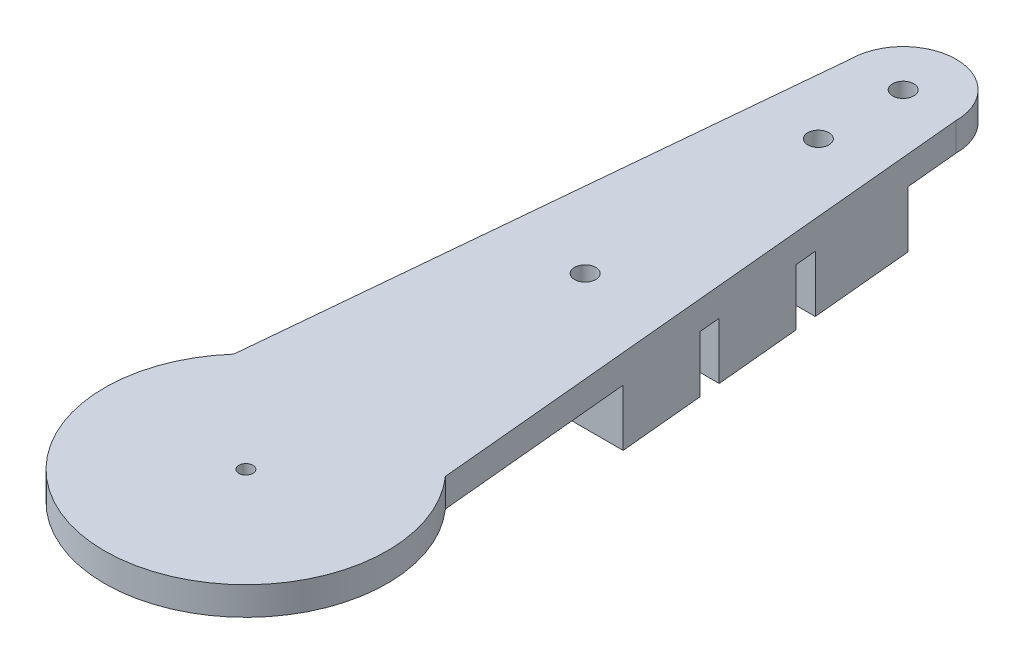
SolidWorks part; units mm, degrees
ref_plane "Front Plane" through (0, 0, 0) normal (0, 0, 1) x (1, 0, 0)
ref_plane "Top Plane" through (0, 0, 0) normal (0, 1, 0) x (1, 0, 0)
ref_plane "Right Plane" through (0, 0, 0) normal (1, 0, 0) x (0, 0, -1)
sketch "Sketch1" plane through (0, 0, 0) normal (0, 0, 1) x (1, 0, 0)
  line L0 (0, -2) -> (10.5, -2)
  line L1 (0, 0) -> (20, 0)
  line L2 (0, 0) -> (0, -2)
  line L3 (10.5, -4) -> (20, -4)
  line L4 (20, 0) -> (20, -4)
  line L5 (10.5, -2) -> (10.5, -4)
  dimension "D1" = 4
  dimension "D2" = 20
  dimension "D3" = 2
  dimension "D4" = 10.5
revolve "Revolve1" add sketch "Sketch1" angle 360 about L2
sketch "Sketch2" plane through (0, 0, 0) normal (0, 1, 0) x (1, 0, 0)
  circle A0 centre (0, 0) radius 1
  dimension "D1" = 2
extrude "Cut-Extrude1" cut sketch "Sketch2" against normal blind 10
sketch "Sketch3" plane through (0, 0, 0) normal (0, 1, 0) x (1, 0, 0)
  line L0 (-7.5, 93) -> (-15, 13)
  line L1 (-15, 13) -> (15, 13)
  line L3 (-7.5, 93) -> (7.5, 93)
  line L5 (7.5, 93) -> (15, 13)
  dimension "D1" = 80
  dimension "D2" = 30
  dimension "D3" = 13
  dimension "D4" = 15
  dimension "D5" = 7.5
extrude "Boss-Extrude1" add sketch "Sketch3" against normal up to surface (4 mm away) up to face at (-20, -4, 0)
sketch "Sketch4" plane through (0, -4, 0) normal (0, -1, 0) x (1, 0, 0)
  line L0 (-12.375, -41) -> (12.375, -41)
  line L1 (12.375, -41) -> (11.25, -53)
  line L2 (11.25, -53) -> (-11.25, -53)
  line L3 (-11.25, -53) -> (-12.375, -41)
  line L4 (-10.9687, -56) -> (10.9688, -56)
  line L5 (-14.976, -13.2559) -> (-7.5, -93) construction
  line L6 (-10.9687, -56) -> (-9.8437, -68) construction
  line L7 (10.9688, -56) -> (9.8438, -68)
  line L8 (9.8438, -68) -> (-9.8437, -68)
  line L9 (-9.8437, -68) -> (-10.9687, -56)
  line L10 (-9.5625, -71) -> (9.5625, -71)
  line L11 (-9.5625, -71) -> (-7.5, -93) construction
  line L12 (9.5625, -71) -> (7.5, -93)
  line L13 (7.5, -93) -> (-7.5, -93)
  line L14 (-7.5, -93) -> (-9.5625, -71)
extrude "Boss-Extrude2" add sketch "Sketch4" along normal blind 8
sketch "Sketch5" plane through (0, 0, 0) normal (0, 1, 0) x (1, 0, 0)
  line L0 (7.5, 93) -> (-7.5, 93) construction
  line L1 (0, 0) -> (0, 93) construction
  circle A0 centre (0, 48) radius 1.5
  circle A1 centre (0, 81) radius 1.5
  dimension "D1" = 3
  dimension "D3" = 3
  dimension "D2" = 45
  dimension "D4" = 12
extrude "Cut-Extrude2" cut sketch "Sketch5" against normal up to surface (12 mm away) up to face at (0, -12, -82)
sketch "Sketch6" plane through (0, -12, 0) normal (0, -1, 0) x (1, 0, 0)
  line L0 (-7.5, -93) -> (7.5, -93) construction
  circle A0 centre (0, -93) radius 7.5
extrude "Boss-Extrude3" add sketch "Sketch6" against normal up to surface (12 mm away)
sketch "Sketch7" plane through (0, -12, 0) normal (0, -1, 0) x (1, 0, 0)
  line L0 (-7.5, -93) -> (7.5, -93) construction
  line L1 (-8.2031, -85.5) -> (8.2031, -85.5)
  line L2 (-9.5625, -71) -> (-7.5, -93) construction
  line L3 (7.5, -93) -> (9.5625, -71) construction
  line L4 (-8.2031, -85.5) -> (-7.5, -93)
  line L5 (8.2031, -85.5) -> (7.5, -93)
  arc A0 (-7.5, -93) -> (7.5, -93) centre (0, -93) ccw
  dimension "D1" = 15
extrude "Cut-Extrude3" cut sketch "Sketch7" against normal blind 8
sketch "Sketch8" plane through (0, 0, 0) normal (0, 1, 0) x (1, 0, 0)
  line L0 (-7.5, 93) -> (7.5, 93) construction
  circle A0 centre (0, 93) radius 1.5
  dimension "D1" = 3
extrude "Cut-Extrude4" cut sketch "Sketch8" against normal up to surface (4 mm away) up to face at (0, -4, -91.125)
